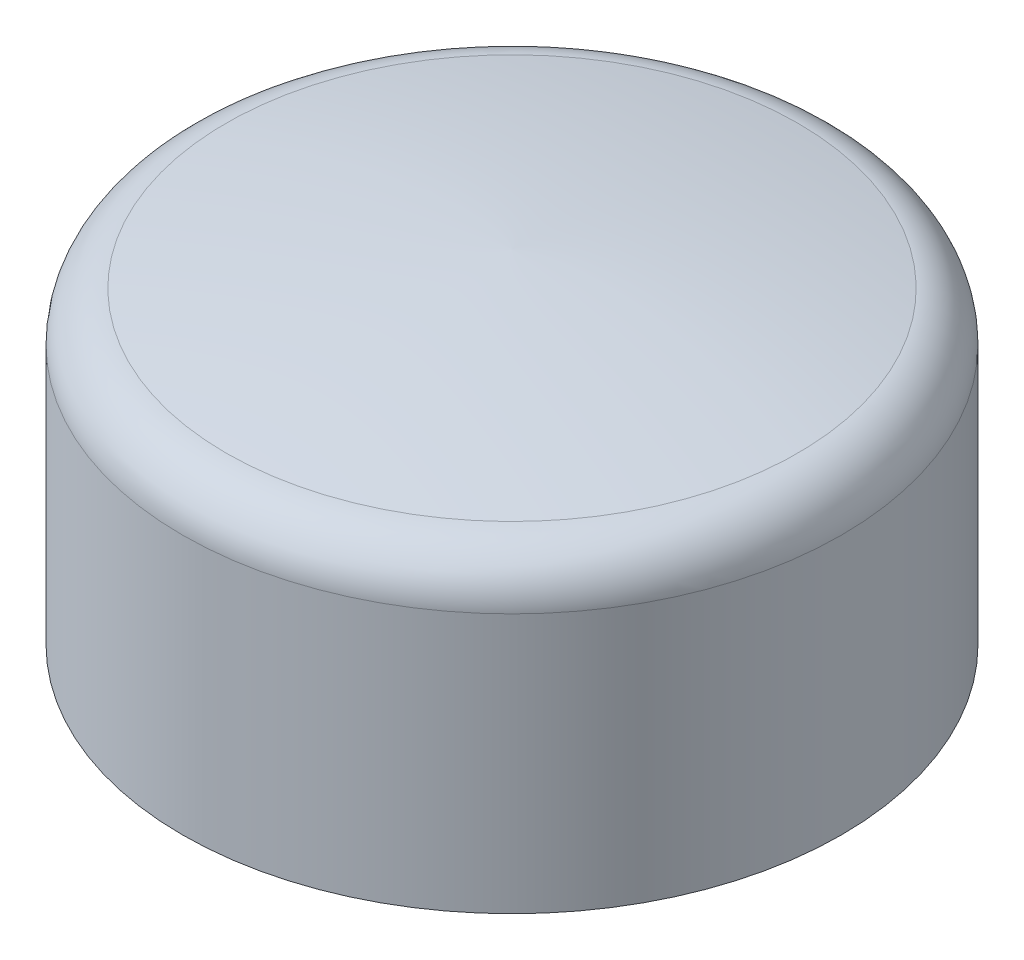
SolidWorks part; units mm, degrees
ref_plane "Front Plane" through (0, 0, 0) normal (0, 0, 1) x (1, 0, 0)
ref_plane "Top Plane" through (0, 0, 0) normal (0, 1, 0) x (1, 0, 0)
ref_plane "Right Plane" through (0, 0, 0) normal (1, 0, 0) x (0, 0, -1)
sketch "Sketch1" plane through (0, 0, 0) normal (0, 0, 1) x (1, 0, 0)
  line L0 (0, 0) -> (0, 31.8321) construction
  line L1 (-33.3, -2.7744) -> (-33.3, 23.4668)
  line L2 (-28.8844, 28.4325) -> (0, 31.8321) construction
  line L3 (-25, -2.7744) -> (-25, 20.7256)
  line L4 (-33.3, -2.7744) -> (-25, -2.7744)
  line L5 (0, 31.8321) -> (0, 23.5256)
  arc A0 (-33.3, 23.4668) -> (-28.8844, 28.4325) centre (-28.3, 23.4668) cw
  arc A1 (-28.8844, 28.4325) -> (0, 31.8321) centre (7.1603, -153.4125) cw
  arc A2 (-25, 20.7256) -> (-25, 20.7256) centre (-25, 20.7256) cw
  arc A3 (-25, 20.7256) -> (0, 23.5256) centre (7.1603, -153.4125) cw
  arc A4 (-25, 20.7256) -> (0.3206, 23.5383) centre (7.1603, -153.4125) cw construction
  dimension "D4" = 5
  dimension "D1" = 11.1065
  dimension "D3" = 33.3
  dimension "D2" = 2.8
  dimension "D6" = 23.5
  dimension "D7" = 25
  dimension "D5" = 8.3
revolve "Revolve1" add sketch "Sketch1" angle 360 about L0
